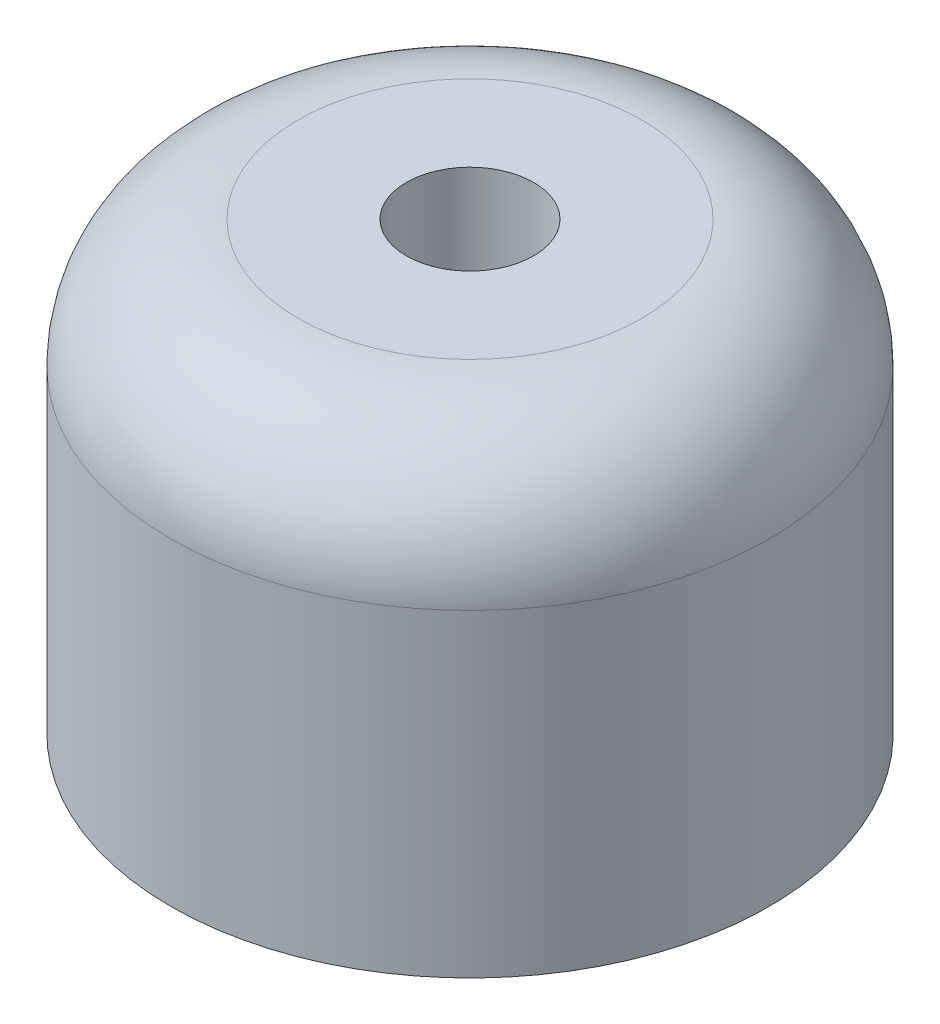
SolidWorks part; units mm, degrees
ref_plane "Front Plane" through (0, 0, 0) normal (0, 0, 1) x (1, 0, 0)
ref_plane "Top Plane" through (0, 0, 0) normal (0, 1, 0) x (1, 0, 0)
ref_plane "Right Plane" through (0, 0, 0) normal (1, 0, 0) x (0, 0, -1)
sketch "Sketch1" plane through (0, 0, 0) normal (0, 1, 0) x (1, 0, 0)
  circle A0 centre (0, 0) radius 235
  dimension "D1" = 470
extrude "Boss-Extrude1" add sketch "Sketch1" along normal blind 350
sketch "Sketch3" plane through (0, 350, 0) normal (0, 1, 0) x (1, 0, 0)
  circle A0 centre (0, 0) radius 50
  dimension "D1" = 100
extrude "Cut-Extrude1" cut sketch "Sketch3" against normal blind 250
fillet "Fillet1" radius 100 1 edges at (0, 350, 235)
